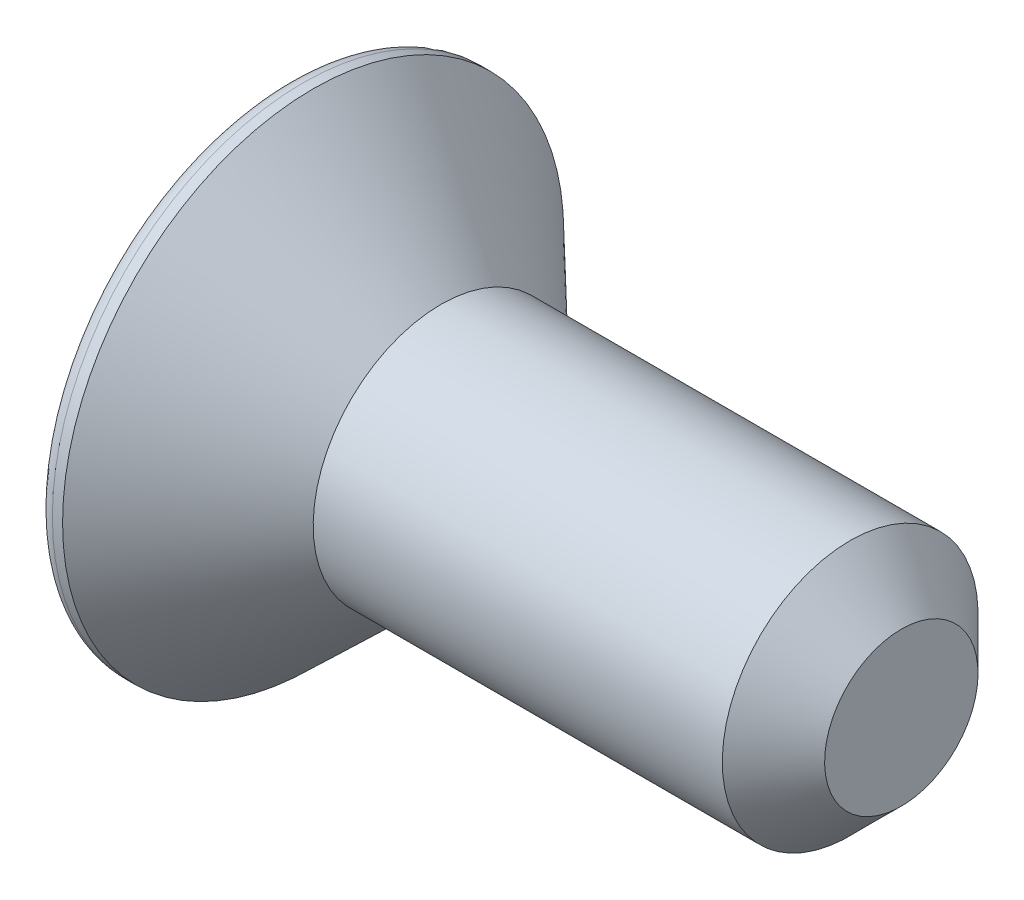
SolidWorks part; units mm, degrees
ref_plane "Спереди" through (0, 0, 0) normal (0, 0, 1) x (1, 0, 0)
ref_plane "Сверху" through (0, 0, 0) normal (0, 1, 0) x (1, 0, 0)
ref_plane "Справа" through (0, 0, 0) normal (1, 0, 0) x (0, 0, -1)
sketch "Эскиз1" plane through (0, 0, 0) normal (0, 0, 1) x (1, 0, 0)
  line L0 (0, 0) -> (0, 4.9)
  line L1 (0.5, 4.9) -> (3, 2.5)
  line L3 (3, 2.5) -> (12, 2.5)
  line L4 (12, 2.5) -> (12, 0)
  line L5 (12, 0) -> (0, 0)
  line L6 (0, 0) -> (12, 0) construction
  line L8 (0, 4.9) -> (0.5, 4.9)
  dimension "D4" = 0.5
  dimension "D1" = 3
  dimension "D2" = 2.5
  dimension "D3" = 4.9
  dimension "D5" = 12
revolve "Повернуть1" add sketch "Эскиз1" angle 360 about L5
cosmetic thread "Условное изображение резьбы1" parameters "D2"=4.11
sketch "Эскиз2" plane through (0, 0, 0) normal (-1, 0, 0) x (0, 0, 1)
  line L1 (0.866, 1.5) -> (-0.866, 1.5)
  line L2 (-0.866, 1.5) -> (-1.7321, 0)
  line L3 (-1.7321, 0) -> (-0.866, -1.5)
  line L4 (-0.866, -1.5) -> (0.866, -1.5)
  line L5 (0.866, -1.5) -> (1.7321, 0)
  line L6 (1.7321, 0) -> (0.866, 1.5)
  circle A0 centre (0, 0) radius 1.5 construction
  dimension "D1" = 3
extrude "Вырез-Вытянуть1" cut sketch "Эскиз2" against normal blind 2
fillet "Скругление1" radius 0.3 1 edges at (0, 4.9, 0)
chamfer "Фаска1" distance 1 angle 45 1 edges at (12, 2.5, 0)
